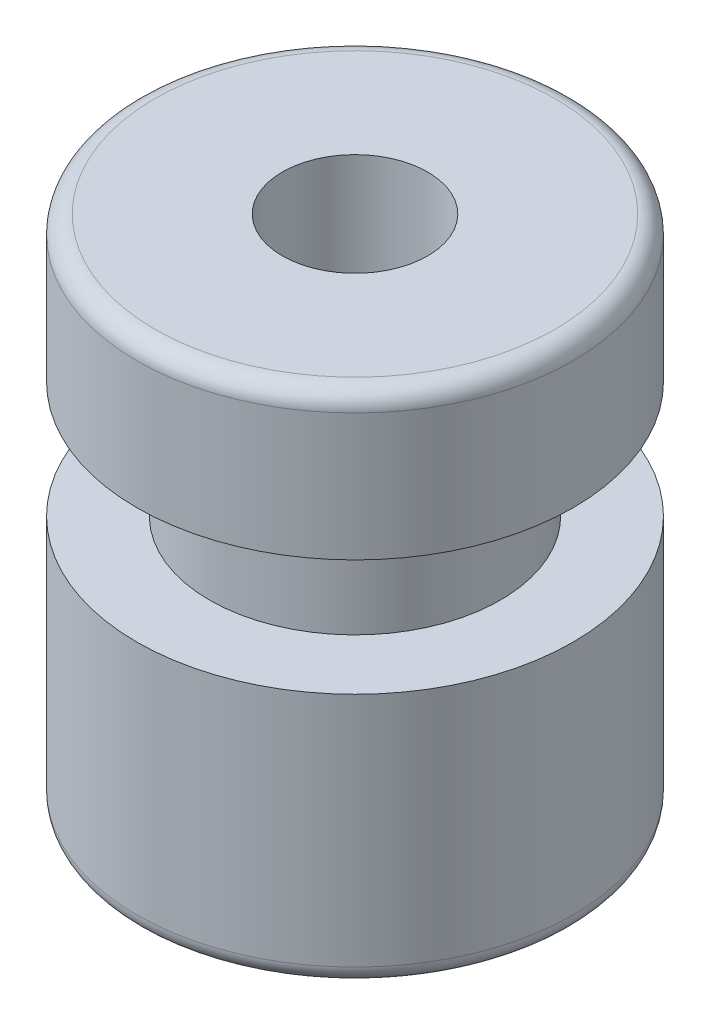
SolidWorks part; units mm, degrees
ref_plane "Front Plane" through (0, 0, 0) normal (0, 0, 1) x (1, 0, 0)
ref_plane "Top Plane" through (0, 0, 0) normal (0, 1, 0) x (1, 0, 0)
ref_plane "Right Plane" through (0, 0, 0) normal (1, 0, 0) x (0, 0, -1)
sketch "Sketch1" plane through (0, 0, 0) normal (0, 1, 0) x (1, 0, 0)
  circle A0 centre (0, 0) radius 1
  circle A1 centre (0, 0) radius 3
  dimension "D1" = 2
  dimension "D2" = 6
extrude "Boss-Extrude1" add sketch "Sketch1" along normal blind 3.5
sketch "Sketch2" plane through (0, 3.5, 0) normal (0, 1, 0) x (1, 0, 0)
  circle A0 centre (0, 0) radius 1 construction
  circle A1 centre (0, 0) radius 1
  circle A2 centre (0, 0) radius 2
  dimension "D1" = 4
extrude "Boss-Extrude2" add sketch "Sketch2" along normal blind 1.6
sketch "Sketch3" plane through (0, 5.1, 0) normal (0, 1, 0) x (1, 0, 0)
  circle A0 centre (0, 0) radius 3 construction
  circle A1 centre (0, 0) radius 3
  circle A2 centre (0, 0) radius 1 construction
  circle A3 centre (0, 0) radius 1
extrude "Boss-Extrude3" add sketch "Sketch3" along normal blind 2
fillet "Fillet1" radius 0.25 2 edges at (0, 0, 3) (0, 7.1, 3)
